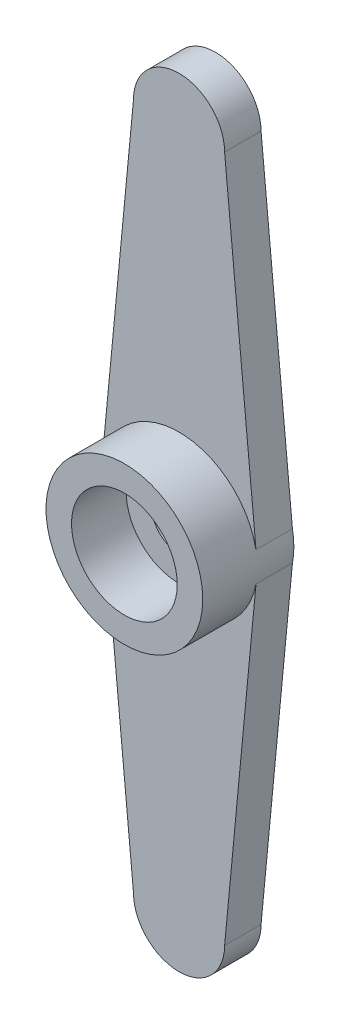
SolidWorks part; units mm, degrees
ref_plane "Front Plane" through (0, 0, 0) normal (0, 0, 1) x (1, 0, 0)
ref_plane "Top Plane" through (0, 0, 0) normal (0, 1, 0) x (1, 0, 0)
ref_plane "Right Plane" through (0, 0, 0) normal (1, 0, 0) x (0, 0, -1)
sketch "Sketch1" plane through (0, 0, 0) normal (0, 0, 1) x (1, 0, 0)
  line L0 (0, 0) -> (0, 21.35) construction
  line L1 (-4.3, 0) -> (5.6747, 0) construction
  line L2 (-2.5, 18.85) -> (-4.2223, 0.8138)
  line L3 (2.5, 18.85) -> (4.2223, 0.8138)
  line L4 (2.5, -18.85) -> (4.2223, -0.8138)
  line L5 (-2.5, -18.85) -> (-4.2223, -0.8138)
  arc A0 (-4.2223, 0.8138) -> (-4.2223, -0.8138) centre (0, 0) ccw
  arc A1 (2.5, 18.85) -> (-2.5, 18.85) centre (0, 18.85) ccw
  arc A2 (2.5, -18.85) -> (-2.5, -18.85) centre (0, -18.85) cw
  arc A3 (4.2223, -0.8138) -> (4.2223, 0.8138) centre (0, 0) ccw
  dimension "D1" = 8.6
  dimension "D3" = 5
  dimension "D2" = 21.35
extrude "Boss-Extrude1" add sketch "Sketch1" along normal blind 2
sketch "Sketch2" plane through (0, 0, 2) normal (0, 0, 1) x (1, 0, 0)
  circle A0 centre (0, 0) radius 4.3
  circle A1 centre (0, 0) radius 2.9
  dimension "D1" = 8.6
  dimension "D2" = 5.8
extrude "Boss-Extrude2" add sketch "Sketch2" along normal blind 3
sketch "Sketch3" plane through (0, 0, 2) normal (0, 0, 1) x (1, 0, 0)
  circle A0 centre (0, 0) radius 1.5
  dimension "D1" = 3
extrude "Cut-Extrude1" cut sketch "Sketch3" against normal through all
